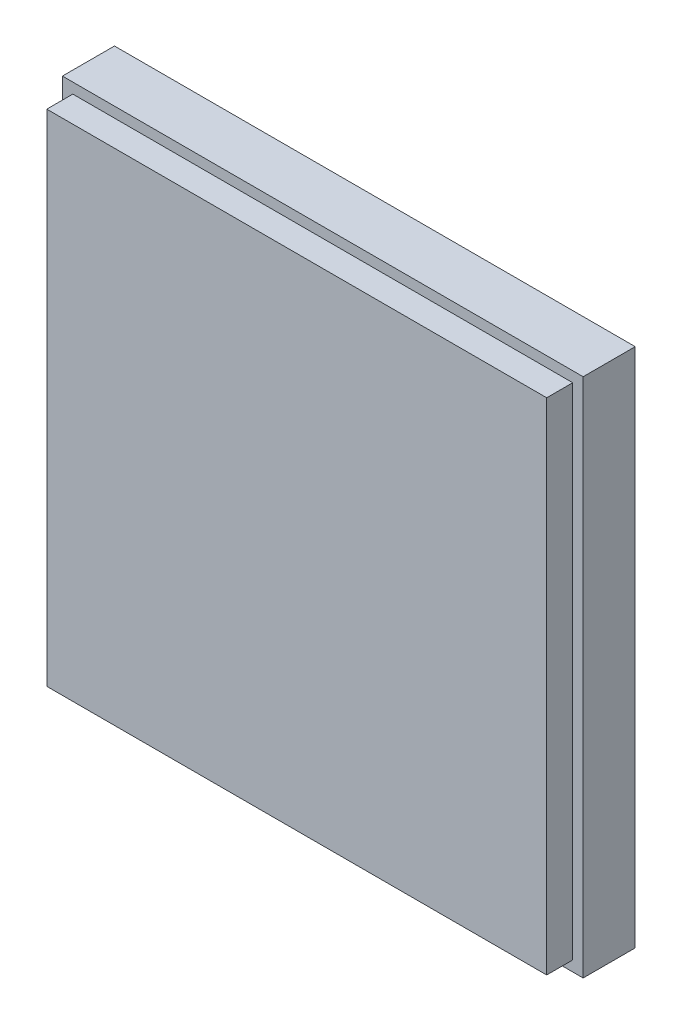
SolidWorks part; units mm, degrees
ref_plane "Front Plane" through (0, 0, 0) normal (0, 0, 1) x (1, 0, 0)
ref_plane "Top Plane" through (0, 0, 0) normal (0, 1, 0) x (1, 0, 0)
ref_plane "Right Plane" through (0, 0, 0) normal (1, 0, 0) x (0, 0, -1)
sketch "Sketch2" plane through (0, 0, 0) normal (0, 0, 1) x (1, 0, 0)
  line L1 (-66.0255, 18.5239) -> (33.9745, 18.5239)
  line L2 (-66.0255, 18.5239) -> (-66.0255, -81.4761)
  line L3 (-66.0255, -81.4761) -> (33.9745, -81.4761)
  line L4 (33.9745, 18.5239) -> (33.9745, -81.4761)
  dimension "D1" = 100
  dimension "D2" = 100
extrude "Boss-Extrude1" add sketch "Sketch2" along normal blind 10
sketch "Sketch3" plane through (0, 0, 10) normal (0, 0, 1) x (1, 0, 0)
  line L0 (33.9745, 18.5239) -> (-66.0255, 18.5239) construction
  line L1 (-64.0255, 16.5239) -> (31.9745, 16.5239)
  line L2 (-64.0255, 16.5239) -> (-64.0255, -79.4761)
  line L3 (-64.0255, -79.4761) -> (31.9745, -79.4761)
  line L4 (31.9745, 16.5239) -> (31.9745, -79.4761)
  line L5 (-66.0255, -81.4761) -> (33.9745, -81.4761) construction
  line L6 (33.9745, -81.4761) -> (33.9745, 18.5239) construction
  line L7 (-66.0255, 18.5239) -> (-66.0255, -81.4761) construction
  dimension "D1" = 2
  dimension "D2" = 2
  dimension "D3" = 2
  dimension "D4" = 2
extrude "Boss-Extrude2" add sketch "Sketch3" along normal blind 5 contours L1 L4 L3 L2
